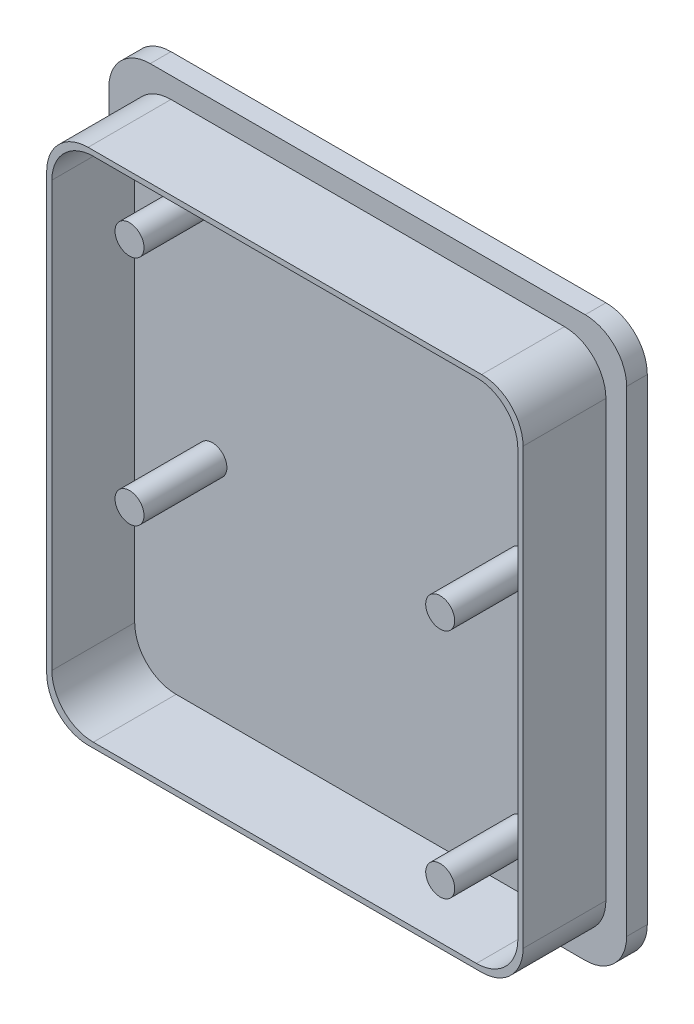
SolidWorks part; units mm, degrees
ref_plane "Front Plane" through (0, 0, 0) normal (0, 0, 1) x (1, 0, 0)
ref_plane "Top Plane" through (0, 0, 0) normal (0, 1, 0) x (1, 0, 0)
ref_plane "Right Plane" through (0, 0, 0) normal (1, 0, 0) x (0, 0, -1)
sketch "Sketch1" plane through (0, 0, 0) normal (0, 0, 1) x (1, 0, 0)
  line L0 (0, 37.1532) -> (0, -34.546) construction
  line L1 (-21, -27) -> (21, -27)
  line L2 (-25, -23) -> (-25, 23)
  line L3 (-21, 27) -> (21, 27)
  line L4 (25, -23) -> (25, 23)
  line L7 (-36.5014, 0) -> (55.4763, 0) construction
  arc A0 (-25, 23) -> (-21, 27) centre (-21, 23) cw
  arc A1 (-25, -23) -> (-21, -27) centre (-21, -23) ccw
  arc A2 (25, 23) -> (21, 27) centre (21, 23) ccw
  arc A3 (25, -23) -> (21, -27) centre (21, -23) cw
  point P0 (0, 0)
  point P2 (-25, 0)
  dimension "D3" = 4
  dimension "D1" = 54
  dimension "D2" = 50
extrude "Boss-Extrude1" add sketch "Sketch1" along normal blind 10
sketch "Sketch3" plane through (0, 0, 10) normal (0, 0, 1) x (1, 0, 0)
  line L0 (-23, 0) -> (23, 0) construction
  line L1 (-19, 25) -> (19, 25)
  line L2 (-23, 21) -> (-23, -21)
  line L3 (-19, -25) -> (19, -25)
  line L4 (23, 21) -> (23, -21)
  line L5 (-18.5, 24.5) -> (18.5, 24.5)
  line L6 (-22.5, 20.5) -> (-22.5, -20.5)
  line L7 (-18.5, -24.5) -> (18.5, -24.5)
  line L8 (22.5, 20.5) -> (22.5, -20.5)
  line L9 (-22.5, 24.5) -> (22.5, -24.5) construction
  line L10 (-22.5, -24.5) -> (22.5, 24.5) construction
  arc A0 (-19, 25) -> (-23, 21) centre (-19, 21) ccw
  arc A1 (23, 21) -> (19, 25) centre (19, 21) ccw
  arc A2 (19, -25) -> (23, -21) centre (19, -21) ccw
  arc A3 (-19, -25) -> (-23, -21) centre (-19, -21) cw
  arc A4 (-18.5, 24.5) -> (-22.5, 20.5) centre (-18.5, 20.5) ccw
  arc A5 (22.5, 20.5) -> (18.5, 24.5) centre (18.5, 20.5) ccw
  arc A6 (-18.5, -24.5) -> (-22.5, -20.5) centre (-18.5, -20.5) cw
  arc A7 (18.5, -24.5) -> (22.5, -20.5) centre (18.5, -20.5) ccw
  circle A8 centre (-15, 19.3) radius 1.4
  circle A9 centre (15, 3.1) radius 1.4
  circle A10 centre (-15, -3.1) radius 1.4
  circle A11 centre (15, -19.3) radius 1.4
  point P0 (0, 0)
  point P15 (0, 0)
  arc M17 (-21, 27) -> (-25, 23) centre (-21, 23) ccw
  line M18 (-25, 23) -> (-25, -23)
  arc M19 (-25, -23) -> (-21, -27) centre (-21, -23) ccw
  line M20 (-21, -27) -> (21, -27)
  arc M21 (21, -27) -> (25, -23) centre (21, -23) ccw
  line M22 (25, -23) -> (25, 23)
  arc M23 (25, 23) -> (21, 27) centre (21, 23) ccw
  line M24 (21, 27) -> (-21, 27)
  dimension "D3" = 4
  dimension "D4" = 4
  dimension "D5" = 4
  dimension "D6" = 4
  dimension "D11" = 4
  dimension "D12" = 4
  dimension "D13" = 4
  dimension "D14" = 4
  dimension "D15" = 2.8
  dimension "D16" = 2.8
  dimension "D25" = 2.8
  dimension "D26" = 2.8
  dimension "D1" = 50
  dimension "D2" = 46
  dimension "D7" = 23
  dimension "D8" = 25
  dimension "D9" = 49
  dimension "D10" = 45
  dimension "D17" = 30
  dimension "D18" = 16.2
  dimension "D19" = 15
  dimension "D20" = 19.3
  dimension "D21" = 30
  dimension "D22" = 16.2
  dimension "D23" = 19.3
  dimension "D24" = 15
extrude "Cut-Extrude2" cut sketch "Sketch3" against normal blind 8 contours L7 A7 L8 A5 L5 A4 L6 A6 A10 A9 A8 A11 | L3 A3 L2 A0 L1 A1 L4 A2 M24 M17 M18 M19 M20 M21 M22 M23
